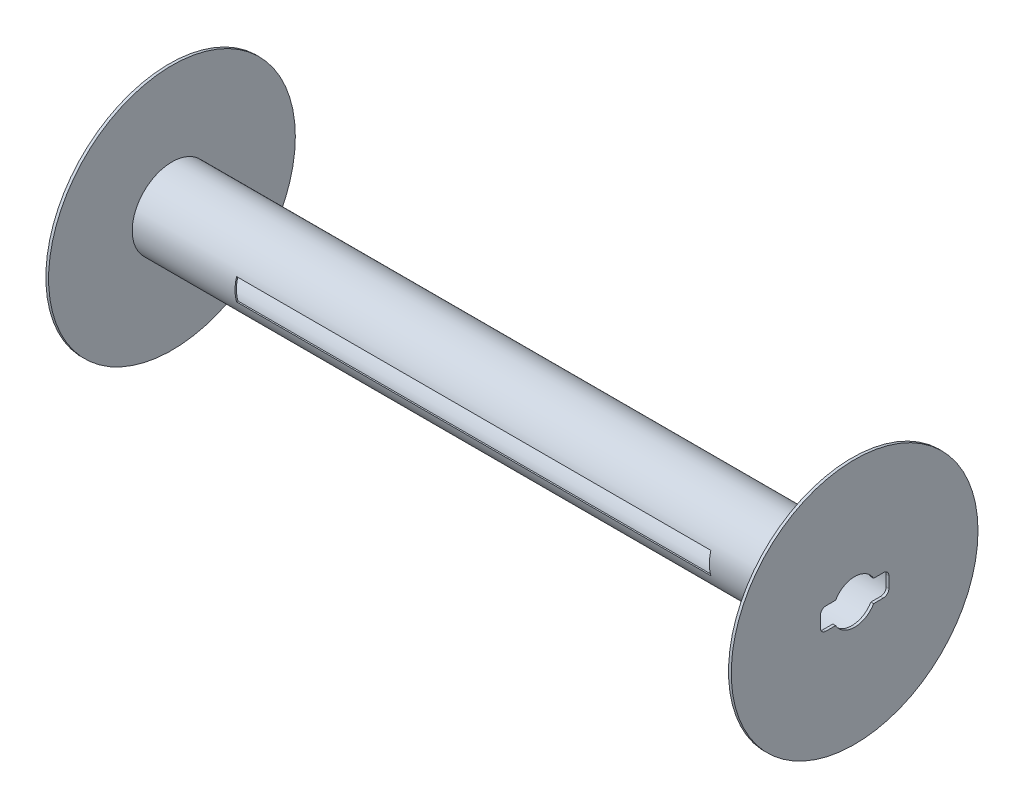
SolidWorks part; units mm, degrees
material "Nickel"
ref_plane "Front Plane" through (0, 0, 0) normal (0, 0, 1) x (1, 0, 0)
ref_plane "Top Plane" through (0, 0, 0) normal (0, 1, 0) x (1, 0, 0)
ref_plane "Right Plane" through (0, 0, 0) normal (1, 0, 0) x (0, 0, -1)
sketch "Sketch1" plane through (0, 0, 0) normal (1, 0, 0) x (0, 0, -1)
  circle A0 centre (0, 0) radius 11.43
  dimension "D1" = 22.86
extrude "Boss-Extrude1" add sketch "Sketch1" along normal blind 0.254
sketch "Sketch2" plane through (0.254, 0, 0) normal (1, 0, 0) x (0, 0, -1)
  circle A0 centre (0, 0) radius 3.683
  circle A1 centre (0, 0) radius 3.556
  dimension "D1" = 7.366
  dimension "D2" = 7.112
extrude "Boss-Extrude2" add sketch "Sketch2" along normal blind 62.992
sketch "Sketch3" plane through (63.246, 0, 0) normal (1, 0, 0) x (0, 0, -1)
  circle A0 centre (0, 0) radius 11.43
  dimension "D1" = 22.86
extrude "Boss-Extrude3" add sketch "Sketch3" along normal blind 0.254
sketch "Sketch4" plane through (0, 0, 0) normal (0, 0, 1) x (1, 0, 0)
  line L0 (0.254, 3.683) -> (63.246, 3.683) construction
  line L5 (0.254, 3.683) -> (0.254, -3.683) construction
ref_plane "Plane1" through (0, 0, 3.683) normal (0, 0, 1) x (1, 0, 0)
sketch "Sketch5" plane through (0, 0, 3.683) normal (0, 0, 1) x (1, 0, 0)
  line L1 (9.779, 1.016) -> (53.721, 1.016)
  line L2 (9.779, 1.016) -> (9.779, -1.016)
  line L3 (9.779, -1.016) -> (53.721, -1.016)
  line L4 (53.721, 1.016) -> (53.721, -1.016)
  dimension "D1" = 43.942
  dimension "D2" = 2.032
extrude "Cut-Extrude1" cut sketch "Sketch5" against normal blind 2.794
ref_plane "Plane2" through (0, 0, -3.683) normal (0, 0, 1) x (1, 0, 0)
sketch "Sketch6" plane through (0, 0, -3.683) normal (0, 0, 1) x (1, 0, 0)
  line L0 (63.246, 3.683) -> (0.254, 3.683) construction
  line L1 (14.351, 1.016) -> (49.149, 1.016)
  line L2 (14.351, 1.016) -> (14.351, -0.964)
  line L3 (14.351, -0.964) -> (49.149, -0.964)
  line L4 (49.149, 1.016) -> (49.149, -0.964)
  line L5 (0.254, 3.683) -> (0.254, -3.683) construction
  point P6 (31.75, 1.016)
  point P13 (31.75, 3.683)
  dimension "D1" = 34.798
  dimension "D2" = 1.98
extrude "Cut-Extrude3" cut sketch "Sketch6" along normal blind 2.794
sketch "Sketch7" plane through (63.5, 0, 0) normal (1, 0, 0) x (0, 0, -1)
  line L4 (3.175, -0.508) -> (3.175, 0.508)
  line L5 (2.667, 1.016) -> (1.7598, 1.016)
  line L6 (2.667, -1.016) -> (1.7598, -1.016)
  line L7 (-2.667, 1.016) -> (-1.7598, 1.016)
  line L9 (-1.7598, -1.016) -> (-2.667, -1.016)
  line L10 (-3.175, -0.508) -> (-3.175, 0.508)
  circle A0 centre (0, 0) radius 2.032
  arc A3 (3.175, -0.508) -> (2.667, -1.016) centre (2.667, -0.508) cw
  arc A4 (2.667, 1.016) -> (3.175, 0.508) centre (2.667, 0.508) cw
  arc A5 (-3.175, -0.508) -> (-2.667, -1.016) centre (-2.667, -0.508) ccw
  arc A6 (-2.667, 1.016) -> (-3.175, 0.508) centre (-2.667, 0.508) ccw
  point P4 (3.175, 0)
  point P14 (3.683, -1.016)
  point P17 (3.683, 1.016)
  point P24 (-3.683, -1.016)
  point P27 (-3.683, 1.016)
  dimension "D1" = 4.064
  dimension "D2" = 2.032
  dimension "D3" = 0.508
  dimension "D4" = 0.508
  dimension "D5" = 0.508
  dimension "D6" = 3.175
  dimension "D7" = 3.175
extrude "Cut-Extrude4" cut sketch "Sketch7" against normal through all contours L7 A6 L10 A5 L9 A0 | A4 L5 A0 L6 A3 L4 | A0
